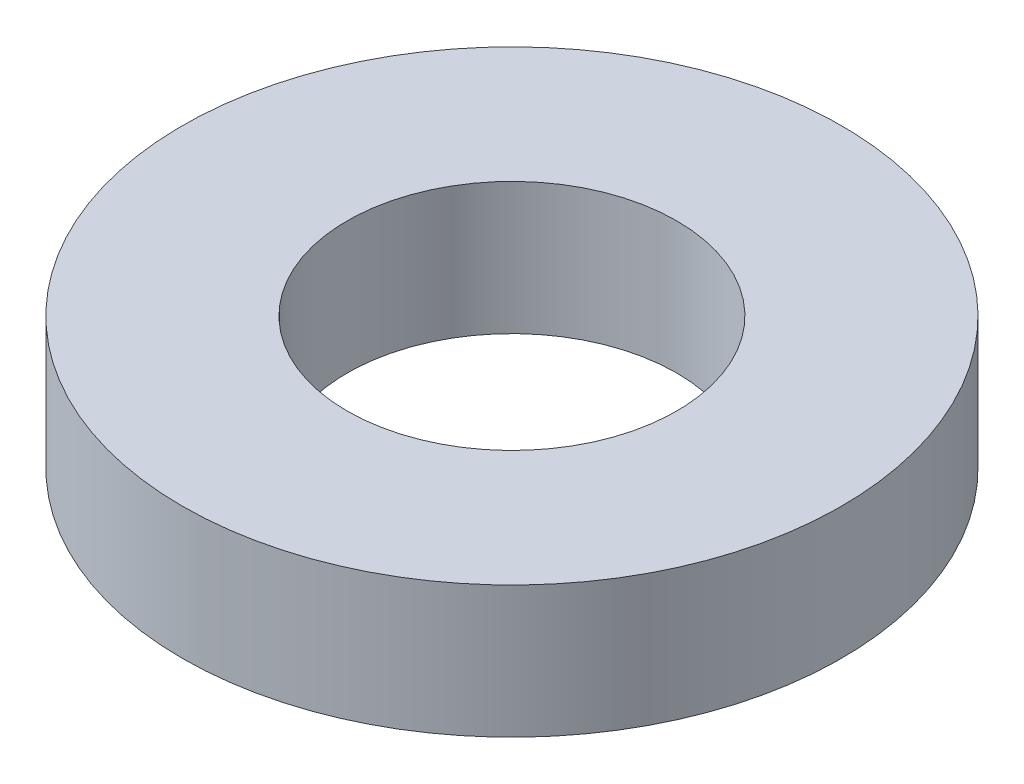
SolidWorks part; units mm, degrees
ref_plane "Alzado" through (0, 0, 0) normal (0, 0, 1) x (1, 0, 0)
ref_plane "Planta" through (0, 0, 0) normal (0, 1, 0) x (1, 0, 0)
ref_plane "Vista lateral" through (0, 0, 0) normal (1, 0, 0) x (0, 0, -1)
sketch "Croquis1" plane through (0, 0, 0) normal (0, 1, 0) x (1, 0, 0)
  circle A0 centre (0, 0) radius 5
  circle A1 centre (0, 0) radius 2.5
extrude "Saliente-Extruir1" add sketch "Croquis1" along normal blind 2
